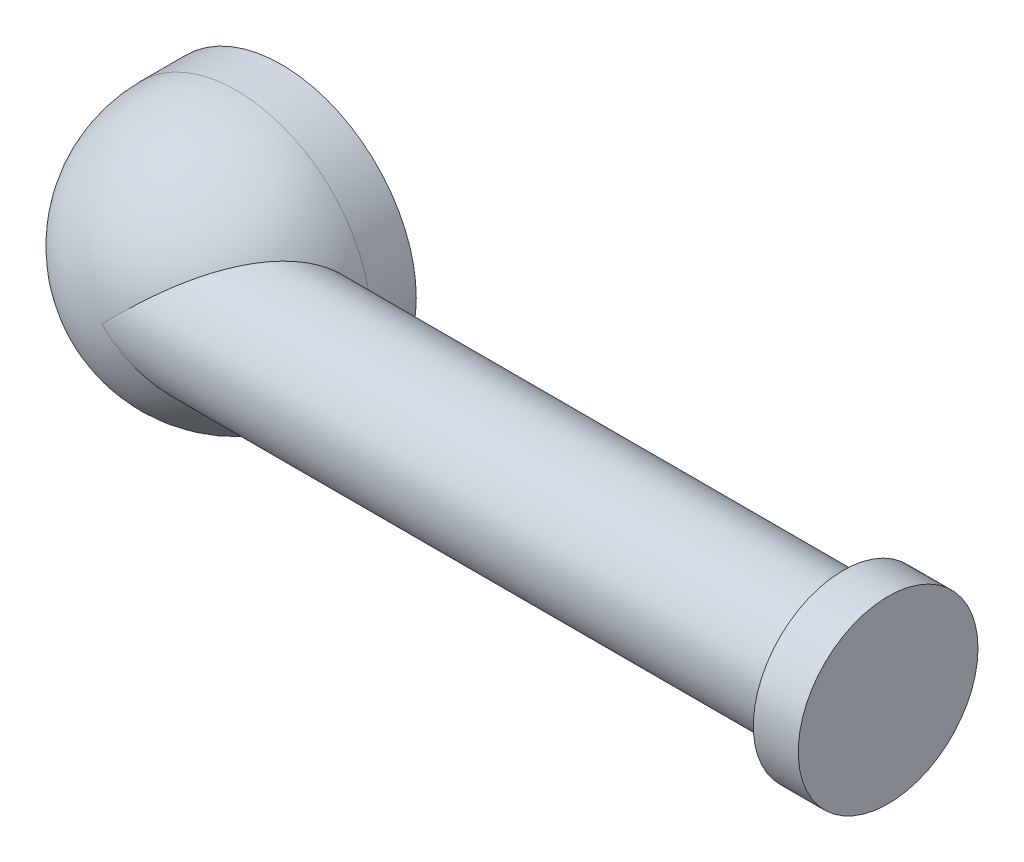
SolidWorks part; units mm, degrees
ref_plane "前视基准面" through (0, 0, 0) normal (0, 0, 1) x (1, 0, 0)
ref_plane "上视基准面" through (0, 0, 0) normal (0, 1, 0) x (1, 0, 0)
ref_plane "右视基准面" through (0, 0, 0) normal (1, 0, 0) x (0, 0, -1)
other "Configuration Table"
sketch "草图1" plane through (0, 0, 0) normal (0, 0, 1) x (1, 0, 0)
  circle A0 centre (0, 0) radius 2
  circle A1 centre (0, 0) radius 3
extrude "凸台-拉伸1" add sketch "草图1" along normal blind 1
sketch "草图2" plane through (0, 0, 0) normal (0, 1, 0) x (1, 0, 0)
  line L0 (0, -4) -> (0, -1)
  line L1 (0, -4) -> (0, -5)
  line L2 (0, -1) -> (3, -1)
  line L4 (-3, -1) -> (3, -1) construction
  arc A1 (0, -4) -> (3, -1) centre (0, -1) ccw
ref_axis "基准轴1" through (0, 0, 4) along (0, 0, 1)
revolve "旋转3" add sketch "草图2" angle 360 about axis through (0, 0, 4) along (0, 0, 1)
sketch "草图4" plane through (0, 0, 0) normal (1, 0, 0) x (0, 0, -1)
  circle A0 centre (-2.5, 0) radius 1.5
extrude "凸台-拉伸2" add sketch "草图4" along normal blind 15
ref_plane "基准面1" through (15, 0, 0) normal (1, 0, 0) x (0, 0, -1)
sketch "草图5" plane through (15, 0, 0) normal (1, 0, 0) x (0, 0, -1)
  circle A0 centre (-2.5, 0) radius 2
extrude "凸台-拉伸3" add sketch "草图5" along normal blind 1 separate body
